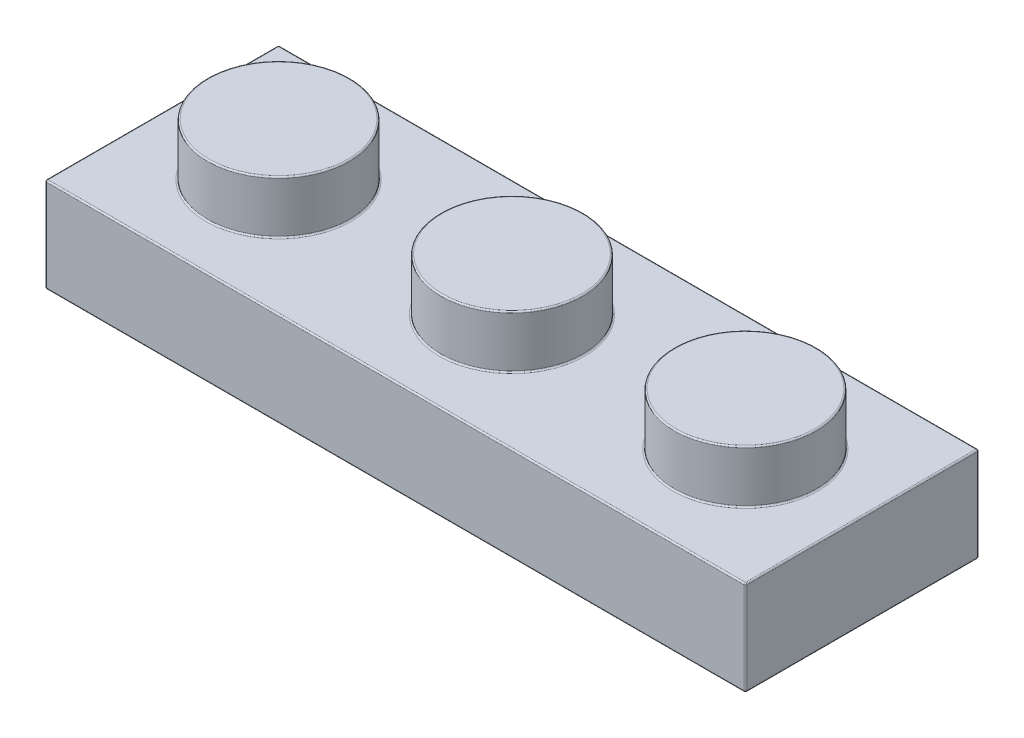
SolidWorks part; units mm, degrees
ref_plane "Front Plane" through (0, 0, 0) normal (0, 0, 1) x (1, 0, 0)
ref_plane "Top Plane" through (0, 0, 0) normal (0, 1, 0) x (1, 0, 0)
ref_plane "Right Plane" through (0, 0, 0) normal (1, 0, 0) x (0, 0, -1)
sketch "Sketch1" plane through (0, 0, 0) normal (0, 1, 0) x (1, 0, 0)
  line L1 (-3.98, 3.98) -> (3.98, 3.98)
  line L2 (-3.98, 3.98) -> (-3.98, -3.98)
  line L3 (-3.98, -3.98) -> (3.98, -3.98)
  line L4 (3.98, 3.98) -> (3.98, -3.98)
  line L5 (-3.98, 3.98) -> (3.98, -3.98) construction
  line L6 (-3.98, -3.98) -> (3.98, 3.98) construction
  point P0 (0, 0)
  dimension "D1" = 7.96
extrude "Extrude1" add sketch "Sketch1" along normal blind 3.22
sketch "Sketch2" plane through (0, 3.22, 0) normal (0, 1, 0) x (1, 0, 0)
  circle A0 centre (0, 0) radius 2.425
  dimension "D1" = 4.85
extrude "Extrude2" add sketch "Sketch2" along normal blind 1.8
pattern_linear "LPattern1" count 3 spacing 7.96 along (1, 0, 0) of "Extrude2", "Extrude1"
shell "Shell1" thickness 1.55
sketch "Sketch3" plane through (0, 1.67, 0) normal (0, -1, 0) x (1, 0, 0)
  line L0 (18.35, 2.43) -> (18.35, -2.43) construction
  line L1 (-2.43, 2.43) -> (18.35, 2.43) construction
  line L2 (-2.43, -2.43) -> (-2.43, 2.43) construction
  line L3 (18.35, -2.43) -> (-2.43, -2.43) construction
  line L4 (18.35, 2.43) -> (18.35, -2.43)
  line L5 (-2.43, 2.43) -> (18.35, 2.43)
  line L6 (-2.43, -2.43) -> (-2.43, 2.43)
  line L7 (18.35, -2.43) -> (-2.43, -2.43)
extrude "Extrude3" cut sketch "Sketch3" against normal blind 0.14
sketch "Sketch4" plane through (0, 1.81, 0) normal (0, -1, 0) x (1, 0, 0)
  line L0 (18.35, 2.43) -> (-2.43, 2.43) construction
  line L1 (0, 2.43) -> (7.96, 2.43) construction
  line L2 (0, 2.43) -> (0, -2.43) construction
  line L3 (0, -2.43) -> (7.96, -2.43) construction
  line L4 (7.96, 2.43) -> (7.96, -2.43) construction
  line L5 (18.35, -2.43) -> (-2.43, -2.43) construction
  line L7 (7.96, 2.43) -> (15.92, 2.43) construction
  line L8 (7.96, 2.43) -> (7.96, -2.43) construction
  line L9 (7.96, -2.43) -> (15.92, -2.43) construction
  line L10 (15.92, 2.43) -> (15.92, -2.43) construction
  circle A0 centre (3.98, 0) radius 1.5
  circle A1 centre (3.98, 0) radius 0.64
  circle A2 centre (11.94, 0) radius 0.64
  circle A3 centre (11.94, 0) radius 1.5
  point P10 (15.92, 0)
  point P12 (0, 0)
  point P14 (7.96, 0)
  point P19 (3.98, 2.43)
  dimension "D1" = 3
  dimension "D2" = 0.86
extrude "Extrude4" add sketch "Sketch4" along normal up to surface (1.81 mm away) up to face at (7.96, 0, 0)
fillet "Fillet1" radius 0.05 44 edges at (11.94, 1.81, 0.64) (11.94, 0, 1.5) (11.94, 0, 0.64) (3.98, 1.81, -0.64) (3.98, 0, 1.5) (3.98, 0, 0.64) (7.96, 1.81, 2.43) (-2.43, 1.81, 0) (7.96, 1.81, -2.43) (18.35, 1.81, 0) (15.92, 1.81, 0.875) (7.96, 1.81, 0.875) (0, 1.81, 0.875) (7.96, 3.47, 0.875) (18.35, 0, 0) (18.35, 0.905, 2.43) (18.35, 0.905, -2.43) (0, 3.47, 0.875) (7.96, 0, -2.43) (-2.43, 0, 0) (7.96, 0, 2.43) (-2.43, 0.905, 2.43) (-2.43, 0.905, -2.43) (15.92, 3.47, 0.875) (7.96, 3.22, 2.425) (7.96, 5.02, 2.425) (19.9, 0, 0) (19.9, 3.22, 0) (19.9, 1.61, -3.98) (19.9, 1.61, 3.98) (0, 3.22, 2.425) (0, 5.02, 2.425) (7.96, 0, -3.98) (-3.98, 0, 0) (7.96, 0, 3.98) (7.96, 3.22, -3.98) (-3.98, 3.22, 0) (7.96, 3.22, 3.98) (-3.98, 1.61, 3.98) (-3.98, 1.61, -3.98) (15.92, 3.22, 2.425) (15.92, 5.02, 2.425) (3.98, 1.81, 1.5) (11.94, 1.81, 1.5)
